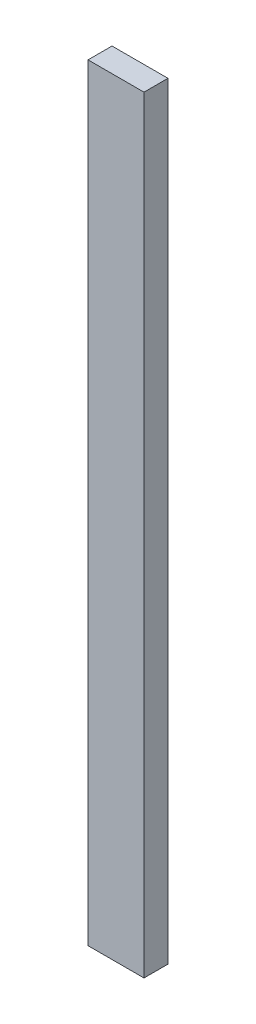
SolidWorks part; units mm, degrees
material "Oak"
ref_plane "Front Plane" through (0, 0, 0) normal (0, 0, 1) x (1, 0, 0)
ref_plane "Top Plane" through (0, 0, 0) normal (0, 1, 0) x (1, 0, 0)
ref_plane "Right Plane" through (0, 0, 0) normal (1, 0, 0) x (0, 0, -1)
sketch "Sketch1" plane through (0, 0, 0) normal (0, 1, 0) x (1, 0, 0)
  line L1 (-44.45, -19.05) -> (44.45, -19.05)
  line L2 (-44.45, -19.05) -> (-44.45, 19.05)
  line L3 (-44.45, 19.05) -> (44.45, 19.05)
  line L4 (44.45, -19.05) -> (44.45, 19.05)
  line L5 (-44.45, -19.05) -> (44.45, 19.05) construction
  line L6 (-44.45, 19.05) -> (44.45, -19.05) construction
  point P0 (0, 0)
  dimension "D1" = 38.1
  dimension "D2" = 88.9
extrude "Boss-Extrude1" add sketch "Sketch1" along normal blind 1219.2 contours L3 L4 L1 L2
